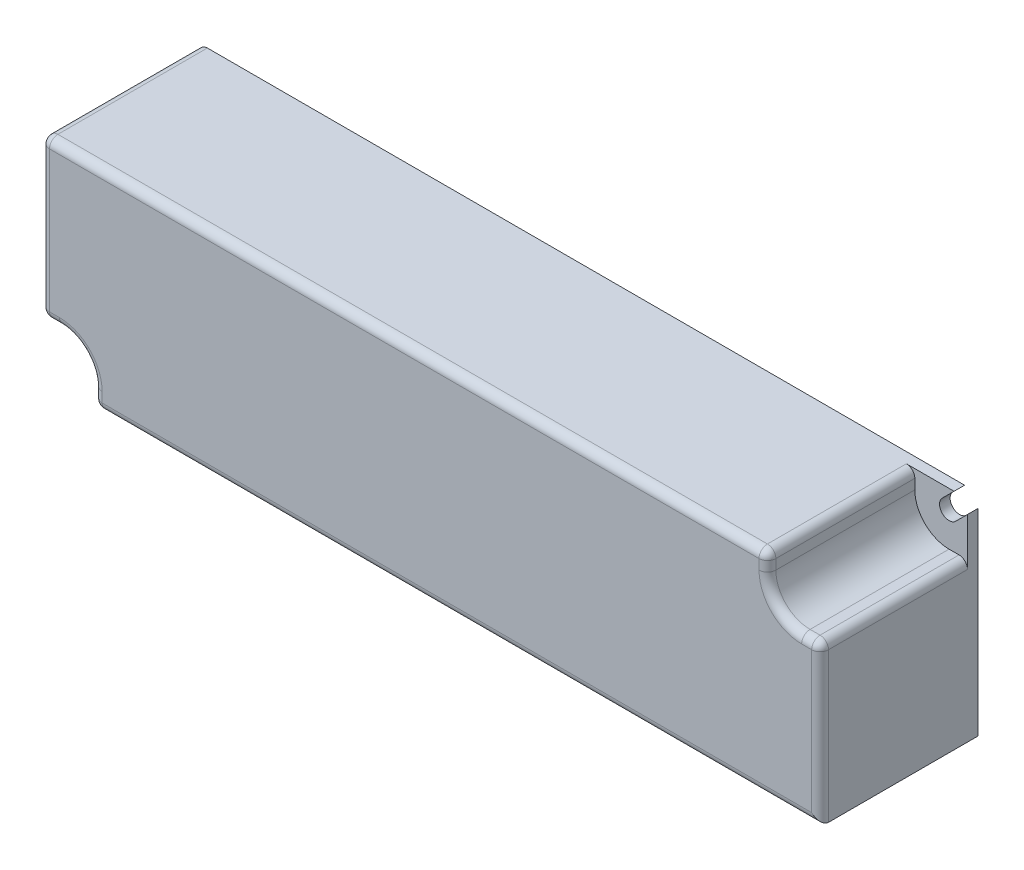
SolidWorks part; units mm, degrees
ref_plane "Front Plane" through (0, 0, 0) normal (0, 0, 1) x (1, 0, 0)
ref_plane "Top Plane" through (0, 0, 0) normal (0, 1, 0) x (1, 0, 0)
ref_plane "Right Plane" through (0, 0, 0) normal (1, 0, 0) x (0, 0, -1)
sketch "Sketch1" plane through (0, 0, 0) normal (0, 0, 1) x (1, 0, 0)
  line L1 (-74, 20) -> (74, 20)
  line L2 (-74, 20) -> (-74, -20)
  line L3 (-74, -20) -> (74, -20)
  line L4 (74, 20) -> (74, -20)
  line L5 (-74, 20) -> (74, -20) construction
  line L6 (-74, -20) -> (74, 20) construction
  point P0 (0, 0)
  dimension "D1" = 148
  dimension "D2" = 40
extrude "Boss-Extrude1" add sketch "Sketch1" along normal blind 30
sketch "Sketch2" plane through (0, 0, 30) normal (0, 0, 1) x (1, 0, 0)
  line L0 (0, 20) -> (0, -20) construction
  line L1 (74, 20) -> (-74, 20) construction
  line L2 (-74, -20) -> (74, -20) construction
  line L3 (74, 0) -> (-74, 0) construction
  line L4 (-74, 20) -> (-74, -20) construction
  line L5 (74, -20) -> (74, 20) construction
  line L6 (70.5, 20) -> (70.5, 16.5) construction
  line L7 (70.5, 16.5) -> (74, 16.5) construction
  line L8 (70.5, 16.5) -> (74, 20) construction
  line L9 (69.2272, 17.7728) -> (73.7272, 22.2728)
  line L10 (71.7728, 15.2272) -> (76.2728, 19.7272)
  line L11 (73.7272, 22.2728) -> (76.2728, 19.7272)
  line L12 (-69.2272, -17.7728) -> (-73.7272, -22.2728)
  line L13 (-71.7728, -15.2272) -> (-76.2728, -19.7272)
  line L14 (-73.7272, -22.2728) -> (-76.2728, -19.7272)
  line L15 (-70.5, -20) -> (-70.5, -16.5) construction
  line L16 (-70.5, -16.5) -> (-74, -16.5) construction
  line L17 (-70.5, -16.5) -> (-74, -20) construction
  arc A0 (69.2272, 17.7728) -> (71.7728, 15.2272) centre (70.5, 16.5) ccw
  arc A1 (-69.2272, -17.7728) -> (-71.7728, -15.2272) centre (-70.5, -16.5) ccw
  point P32 (0, 0)
  dimension "D3" = 2
  dimension "D2" = 3.6
  dimension "D1" = 3.5
extrude "Cut-Extrude1" cut sketch "Sketch2" against normal blind 30
sketch "Sketch3" plane through (0, 0, 30) normal (0, 0, 1) x (1, 0, 0)
  line L0 (64, 27.7068) -> (64, 16.5)
  line L2 (70.5, 10) -> (82.0364, 10)
  line L4 (71.4544, 20) -> (-74, 20) construction
  line L5 (74, -20) -> (74, 17.4544) construction
  line L6 (64, 27.7068) -> (82.0364, 10)
  line L7 (-64, -27.7068) -> (-64, -16.5)
  line L8 (-70.5, -10) -> (-82.0364, -10)
  line L9 (-64, -27.7068) -> (-82.0364, -10)
  arc A0 (64, 16.5) -> (70.5, 10) centre (70.5, 16.5) ccw
  arc A1 (-64, -16.5) -> (-70.5, -10) centre (-70.5, -16.5) ccw
  point P18 (0, 0)
  dimension "D1" = 10
  dimension "D2" = 10
  dimension "D3" = 2
extrude "Cut-Extrude2" cut sketch "Sketch3" against normal blind 28
fillet "Fillet1" radius 1.6 15 edges at (64, 18.25, 30) (72.25, 10, 30) (-64, -18.25, 30) (-72.25, -10, 30) (74, 10, 16) (74, -5, 30) (65.9038, 11.9038, 30) (64, 20, 16) (-74, 20, 15) (-5, 20, 30) (5, -20, 30) (-74, -10, 16) (-64, -20, 16) (-65.9038, -11.9038, 30) (-74, 5, 30)
